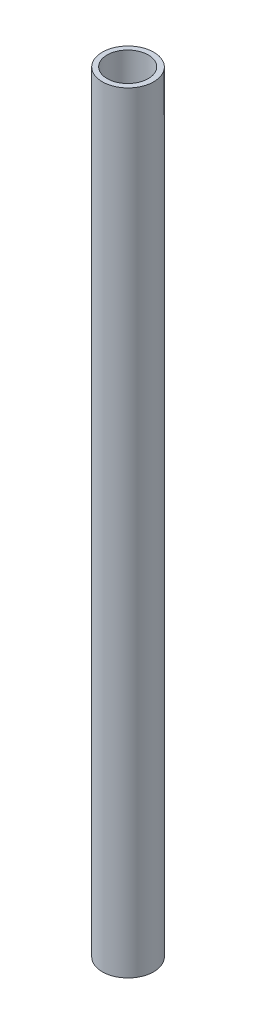
SolidWorks part; units mm, degrees
ref_plane "Front Plane" through (0, 0, 0) normal (0, 0, 1) x (1, 0, 0)
ref_plane "Top Plane" through (0, 0, 0) normal (0, 1, 0) x (1, 0, 0)
ref_plane "Right Plane" through (0, 0, 0) normal (1, 0, 0) x (0, 0, -1)
sketch "Sketch1" plane through (0, 0, 0) normal (0, 0, 1) x (1, 0, 0)
  line L0 (0, 0) -> (5, 0)
  line L2 (0, 150) -> (5, 150)
  line L3 (5, 150) -> (5, 0)
  line L4 (-0.4375, 0) -> (-0.0625, 150) construction
  line L5 (-0.5, -50) -> (-0.5, 0) construction
  line L7 (0, 0) -> (0, 150)
  line L8 (-0.5, -50) -> (-0.5, 200) construction
  line L9 (-0.5, 200) -> (0, 200) construction
  arc A0 (-0.4375, 0) -> (-0.5, -50) centre (19999.5547, -50) ccw construction
  arc A1 (-0.0625, 150) -> (0, 200) centre (-20000.0547, 200) ccw construction
  point P0 (-0.5707, 150)
  dimension "D1" = 5
  dimension "D2" = 150
  dimension "D3" = 50
  dimension "D4" = 0.5
revolve "Revolve1" add sketch "Sketch1" angle 360 about L7
ref_plane "Plane1" through (5, 150, 0) normal (0.0025, 1, 0) x (1, -0.0025, 0)
sketch "Sketch2" plane through (5, 150, 0) normal (0.0025, 1, 0) x (1, -0.0025, 0)
  circle A0 centre (-5.0625, 0) radius 4
  point P2 (0, 0)
  point P3 (0, 0)
  dimension "D1" = 8
extrude "Cut-Extrude1" cut sketch "Sketch2" against normal through all
